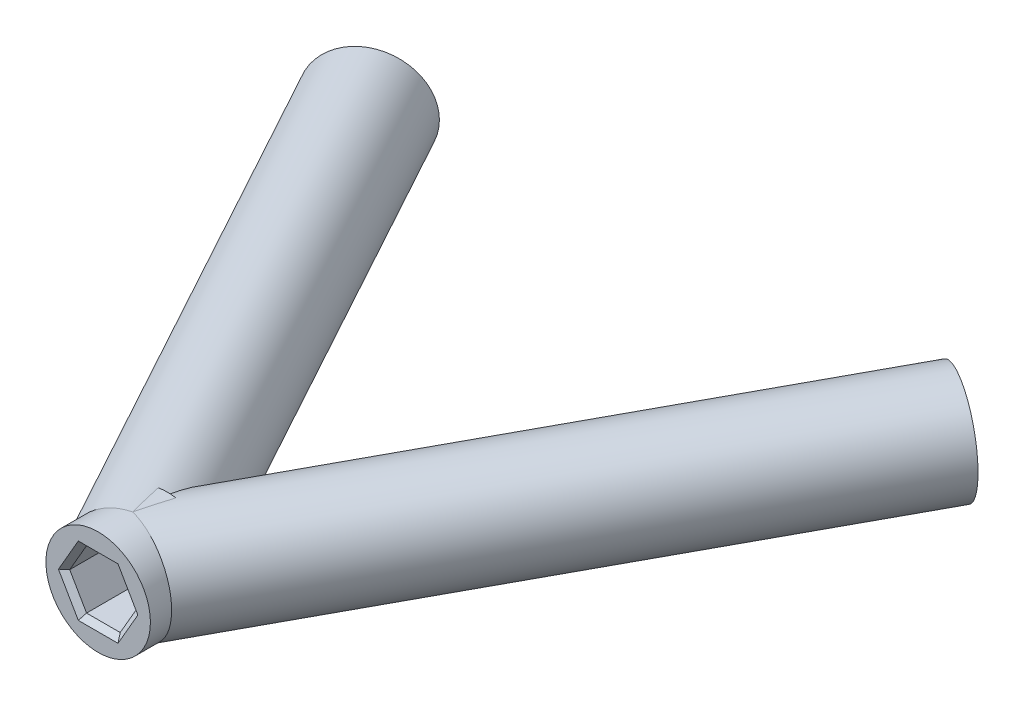
SolidWorks part; units mm, degrees
material "ABS"
ref_plane "Front Plane" through (0, 0, 0) normal (0, 0, 1) x (1, 0, 0)
ref_plane "Top Plane" through (0, 0, 0) normal (0, 1, 0) x (1, 0, 0)
ref_plane "Right Plane" through (0, 0, 0) normal (1, 0, 0) x (0, 0, -1)
sketch "Sketch1" plane through (0, 0, 0) normal (0, 1, 0) x (1, 0, 0)
  line L0 (0, 0) -> (36.1483, 87.2697) construction
  line L1 (0, 0) -> (-35.5896, 85.9208) construction
  line L2 (0, 0) -> (0, 97.1253) construction
  line L11 (0, 0) -> (0, -18.024) construction
  line L12 (0, 17.5) -> (0, 24.1)
  point P3 (-24.4917, 59.1283)
  point P6 (25.0505, 60.4772)
  point P8 (0, 17.5)
  point P9 (-27.0175, 65.2259)
  point P10 (27.5762, 66.5748)
  point P26 (0, 15.6788)
  point P27 (31.3933, 91.469)
  point P28 (36.9366, 89.1729)
  point P29 (42.4799, 86.8768)
  point P30 (0, -15.6788)
  dimension "D8" = 17.5
  dimension "D10" = 22.4
  dimension "D1" = 94.46
  dimension "D2" = 93
  dimension "D3" = 45
  dimension "D4" = 22.5
  dimension "D5" = 29
  dimension "D6" = 29
  dimension "D7" = 6.6
  dimension "D9" = 22.4
revolve "Revolve-Thin1" add sketch "Sketch1" angle 360 about L12 wall 5
sketch "Sketch18" plane through (0, 0, -17.5) normal (0, 0, 1) x (1, 0, 0)
  line L1 (1.6108, 2.79) -> (-1.6108, 2.79)
  line L2 (-1.6108, 2.79) -> (-3.2216, 0)
  line L3 (-3.2216, 0) -> (-1.6108, -2.79)
  line L4 (-1.6108, -2.79) -> (1.6108, -2.79)
  line L5 (1.6108, -2.79) -> (3.2216, 0)
  line L6 (3.2216, 0) -> (1.6108, 2.79)
  circle A0 centre (0, 0) radius 2.79 construction
  dimension "D1" = 5.58
sketch "Sketch19" plane through (0, 0, 0) normal (0, 1, 0) x (1, 0, 0)
  line L0 (0, 17.5) -> (0, 24.1) construction
  line L1 (0, 17.5) -> (0, 24.1) construction
  line L2 (-35.5896, 85.9208) -> (0, 20.8) construction
  line L3 (0, 20.8) -> (36.1483, 87.2697) construction
  line L5 (-27.1971, 70.5645) -> (0, 20.8)
  line L6 (0, 0) -> (0, 97.1253) construction
  line L8 (0, 0) -> (0, 97.1253) construction
  point P2 (0, 20.8)
  point P6 (-27.1971, 70.5645)
  point P9 (27.7876, 71.896)
  point P11 (0, 87.2697)
  dimension "D1" = 17.5
  dimension "D2" = 17.5
  dimension "D3" = 87.2697
  dimension "D4" = 36.1483
  dimension "D5" = 35.5896
  dimension "D6" = 28.539
  dimension "D7" = 28.657
  dimension "D8" = 56.7114
  dimension "D9" = 58.1632
sketch "Sketch20" plane through (0, 0, 0) normal (0, 1, 0) x (1, 0, 0)
  line L0 (36.1483, 87.2697) -> (0, 20.8) construction
  line L1 (0, 17.5) -> (0, 24.1) construction
  line L2 (25.4466, 67.5914) -> (0, 20.8)
  point P5 (25.4466, 67.5914)
  dimension "D1" = 22.4
sketch3d "3DSketch1"
  line L0 (-27.1971, 0, -70.5645) -> (0, 0, -20.8) construction
sketch "Sketch21" plane through (-35.9502, 0, -65.7807) normal (0.4796, 0, 0.8775) x (0.8775, 0, -0.4796)
  circle A0 centre (9.9751, 0) radius 5
  dimension "D1" = 10
extrude "Boss-Extrude1" add sketch "Sketch21" along normal up to next
sketch3d "3DSketch2"
  line L1 (0, 0, -20.8) -> (36.1483, 0, -87.2697) construction
sketch "Sketch22" plane through (36.5174, 0, -67.1485) normal (-0.4778, 0, 0.8785) x (0.8785, 0, 0.4778)
  circle A0 centre (-9.9373, 0) radius 5
  dimension "D1" = 10
extrude "Boss-Extrude2" add sketch "Sketch22" along normal up to next
sketch "Sketch24" plane through (0, 0, -24.1) normal (0, 0, -1) x (-1, 0, 0)
sketch3d "3DSketch3"
  line L0 (0, 0, 0) -> (0, 0, -97.1253) construction
  line L1 (0, 0, 0) -> (-35.5896, 0, -85.9208) construction
sketch "Sketch29" plane through (-35.9502, 0, -65.7807) normal (-0.4796, 0, -0.8775) x (-0.8775, 0, 0.4796)
  line L0 (-9.9751, 5) -> (-9.9751, -5) construction
  line L1 (-7.09, 1.4335) -> (-9.774, 3.2153)
  line L2 (-9.774, 3.2153) -> (-12.6591, 1.7818)
  line L3 (-12.6591, 1.7818) -> (-12.8602, -1.4335)
  line L4 (-12.8602, -1.4335) -> (-10.1761, -3.2153)
  line L5 (-10.1761, -3.2153) -> (-7.291, -1.7818)
  line L6 (-7.291, -1.7818) -> (-7.09, 1.4335)
  line L7 (-14.9751, 0) -> (-4.9751, 0) construction
  line L8 (-9.774, 3.2153) -> (-10.1761, -3.2153) construction
  circle A0 centre (-9.9751, 0) radius 2.79 construction
  circle A1 centre (-9.9751, 0) radius 5 construction
  arc A2 (-11.5546, 4.7439) -> (-11.5546, -4.7439) centre (-9.9751, 0) ccw construction
  dimension "D1" = 5.58
  dimension "D2" = 3.578
extrude "Cut-Extrude3" cut sketch "Sketch29" against normal blind 6.6
sketch "Sketch30" plane through (36.5174, 0, -67.1485) normal (0.4778, 0, -0.8785) x (-0.8785, 0, -0.4778)
  line L0 (9.9373, 5) -> (9.9373, -5) construction
  line L1 (12.6213, 1.7818) -> (9.7362, 3.2153)
  line L2 (9.7362, 3.2153) -> (7.0522, 1.4335)
  line L3 (7.0522, 1.4335) -> (7.2532, -1.7818)
  line L4 (7.2532, -1.7818) -> (10.1383, -3.2153)
  line L5 (10.1383, -3.2153) -> (12.8224, -1.4335)
  line L6 (12.8224, -1.4335) -> (12.6213, 1.7818)
  line L7 (4.9373, 0) -> (14.9373, 0) construction
  line L8 (9.7362, 3.2153) -> (10.1383, -3.2153) construction
  circle A0 centre (9.9373, 0) radius 2.79 construction
  circle A1 centre (9.9373, 0) radius 5 construction
  arc A2 (9.9373, 5) -> (9.9373, -5) centre (9.9373, 0) ccw construction
  arc A3 (11.5168, -4.7439) -> (11.5168, 4.7439) centre (9.9373, 0) ccw construction
  dimension "D1" = 5.58
  dimension "D2" = 3.578
extrude "Cut-Extrude4" cut sketch "Sketch30" against normal blind 6.6
extrude "Cut-Extrude5" cut sketch "Sketch18" against normal blind 6.6
chamfer "Chamfer2" distance 0.5 angle 45 18 edges at (0, 2.79, -17.5) (2.4162, 1.395, -17.5) (2.4162, -1.395, -17.5) (0, -2.79, -17.5) (-2.4162, -1.395, -17.5) (-2.4162, 1.395, -17.5) (-29.6405, -0.1741, -69.2291) (-28.2865, -2.4986, -69.9691) (-25.843, -2.3244, -71.3045) (-24.7536, 0.1741, -71.8999) (-26.1077, 2.4986, -71.1599) (-28.5512, 2.3244, -69.8245) (25.3414, 0.1741, -73.2263) (26.432, -2.3244, -72.6332) (28.8782, -2.4986, -71.3029) (30.2338, -0.1741, -70.5657) (29.1432, 2.3244, -71.1588) (26.697, 2.4986, -72.4891)
